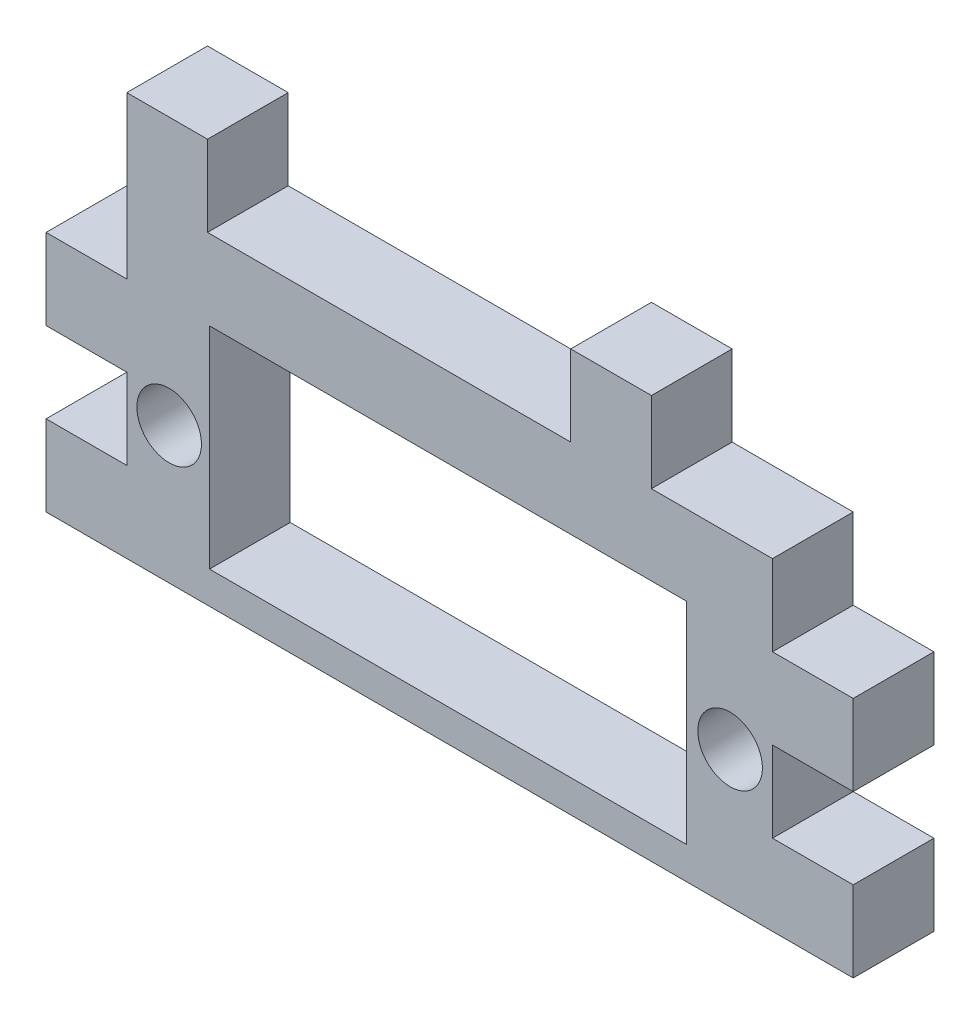
SolidWorks part; units mm, degrees
ref_plane "Plan de face" through (0, 0, 0) normal (0, 0, 1) x (1, 0, 0)
ref_plane "Plan de dessus" through (0, 0, 0) normal (0, 1, 0) x (1, 0, 0)
ref_plane "Plan de droite" through (0, 0, 0) normal (1, 0, 0) x (0, 0, -1)
sketch "Esquisse1" plane through (0, 0, 0) normal (0, 0, 1) x (1, 0, 0)
  line L1 (-66.0216, -12.9076) -> (-41.0216, -12.9076)
  line L2 (-66.0216, -12.9076) -> (-66.0216, -37.9076)
  line L3 (-66.0216, -37.9076) -> (-41.0216, -37.9076)
  line L4 (-41.0216, -12.9076) -> (-41.0216, -37.9076)
extrude "Boss.-Extru.1" add sketch "Esquisse1" along normal blind 5
sketch "Esquisse3" plane through (0, 0, 0) normal (0, 0, -1) x (-1, 0, 0)
  line L0 (66.0216, -12.9076) -> (66.0216, -17.9076)
  line L1 (41.0216, -12.9076) -> (66.0216, -12.9076) construction
  line L3 (66.0216, -12.9076) -> (66.0216, -37.9076) construction
  line L4 (41.0216, -32.9076) -> (46.0216, -32.9076)
  line L5 (66.0216, -17.9076) -> (46.0216, -17.9076)
  line L6 (41.0216, -32.9076) -> (41.0216, -27.9076)
  line L8 (46.0216, -17.9076) -> (46.0216, -22.9076)
  line L9 (46.0216, -22.9076) -> (41.0216, -22.9076)
  line L10 (41.0216, -37.9076) -> (41.0216, -12.9076) construction
  line L15 (41.0216, -22.9076) -> (41.0216, -12.9076)
  line L16 (41.0216, -12.9076) -> (66.0216, -12.9076)
  line L17 (41.0216, -27.9076) -> (46.0216, -27.9076)
  line L18 (46.0216, -32.9076) -> (46.0216, -27.9076)
  dimension "D1" = 0
  dimension "D2" = 5
  dimension "D3" = 5
  dimension "D4" = 5
  dimension "D5" = 5
  dimension "D6" = 5
extrude "Enlèv. mat.-Extru.1" cut sketch "Esquisse3" against normal blind 5
mirror "Symétrie1" about plane through (-66.0216, -12.9076, 5) normal (1, 0, 0) of "Enlèv. mat.-Extru.1", "Boss.-Extru.1"
sketch "Esquisse4" plane through (0, 0, 0) normal (0, 0, -1) x (-1, 0, 0)
  line L0 (91.0216, -37.9076) -> (41.0216, -37.9076) construction
  line L1 (80.8966, -35.9076) -> (51.3466, -35.9076)
  line L2 (80.8966, -35.9076) -> (80.8966, -22.8576)
  line L3 (80.8966, -22.8576) -> (51.3466, -22.8576)
  line L4 (51.3466, -35.9076) -> (51.3466, -22.8576)
  line L5 (46.0216, -32.9076) -> (46.0216, -27.9076) construction
  line L6 (86.0216, -32.9076) -> (86.0216, -27.9076) construction
  line L9 (41.0216, -27.9076) -> (41.0216, -22.9076) construction
  line L11 (91.0216, -37.9076) -> (41.0216, -37.9076) construction
  line L12 (91.0216, -37.9076) -> (41.0216, -37.9076) construction
  circle A0 centre (83.3966, -29.4576) radius 2
  circle A1 centre (48.6466, -29.4576) radius 2
  point P10 (41.0216, -25.4076)
  dimension "D2" = 2.5
  dimension "D1" = 2
  dimension "D3" = 29.55
  dimension "D4" = 10.325
  dimension "D5" = 2
  dimension "D6" = 2.7
  dimension "D7" = 8.45
  dimension "D8" = 8.45
  dimension "D9" = 2.625
  dimension "D10" = 2.625
extrude "Enlèv. mat.-Extru.2" cut sketch "Esquisse4" along direction (0, 0, 1) on the side against the normal up to surface (5 mm away)
sketch "Esquisse5" plane through (0, -17.9076, 0) normal (0, 1, 0) x (1, 0, 0)
  line L0 (-46.0216, 0) -> (-86.0216, 0) construction
  line L1 (-86.0216, 0) -> (-81.0216, 0)
  line L2 (-86.0216, 0) -> (-86.0216, -5)
  line L3 (-86.0216, -5) -> (-81.0216, -5)
  line L4 (-81.0216, 0) -> (-81.0216, -5)
  line L5 (-58.5216, 0) -> (-53.5216, 0)
  line L6 (-58.5216, 0) -> (-58.5216, -5)
  line L7 (-58.5216, -5) -> (-53.5216, -5)
  line L8 (-53.5216, 0) -> (-53.5216, -5)
  line L9 (-46.0216, -5) -> (-86.0216, -5) construction
  line L11 (-46.0216, -5) -> (-46.0216, 0) construction
  dimension "D1" = 5
  dimension "D2" = 7.5
extrude "Boss.-Extru.2" add sketch "Esquisse5" along normal blind 5
